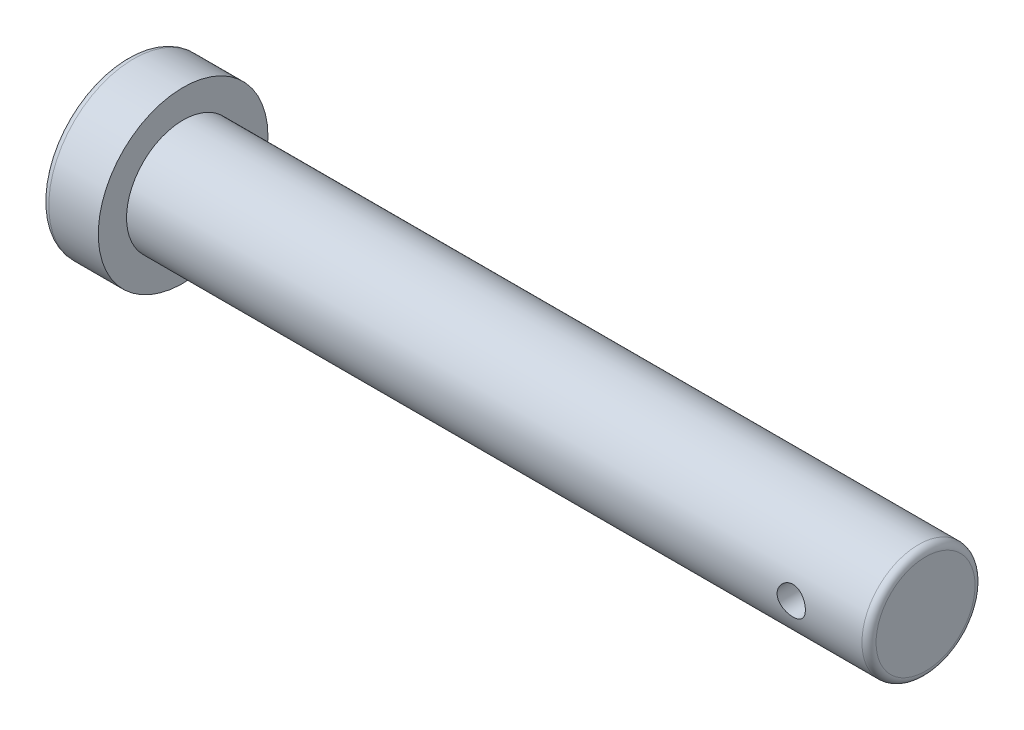
SolidWorks part; units mm, degrees
ref_plane "Front Plane" through (0, 0, 0) normal (0, 0, 1) x (1, 0, 0)
ref_plane "Top Plane" through (0, 0, 0) normal (0, 1, 0) x (1, 0, 0)
ref_plane "Right Plane" through (0, 0, 0) normal (1, 0, 0) x (0, 0, -1)
sketch "Sketch2" plane through (0, 0, 0) normal (1, 0, 0) x (0, 0, -1)
  circle A1 centre (0, 0) radius 12
  dimension "D2" = 24
extrude "Boss-Extrude1" add sketch "Sketch2" along normal mid plane 8
sketch "Sketch3" plane through (4, 0, 0) normal (1, 0, 0) x (0, 0, -1)
  circle A0 centre (0, 0) radius 8
  dimension "D1" = 16
extrude "Boss-Extrude2" add sketch "Sketch3" along normal blind 105
fillet "Fillet1" radius 1 1 edges at (-4, 0, -12)
fillet "Fillet2" radius 1 1 edges at (109, 0, -8)
sketch "Sketch4" plane through (0, 0, 0) normal (0, 0, 1) x (1, 0, 0)
  line L0 (4, -12) -> (4, 12) construction
  circle A0 centre (98, 0) radius 2
  dimension "D1" = 4
  dimension "D2" = 94
extrude "Cut-Extrude1" cut sketch "Sketch4" against normal mid plane 20 contours A0
